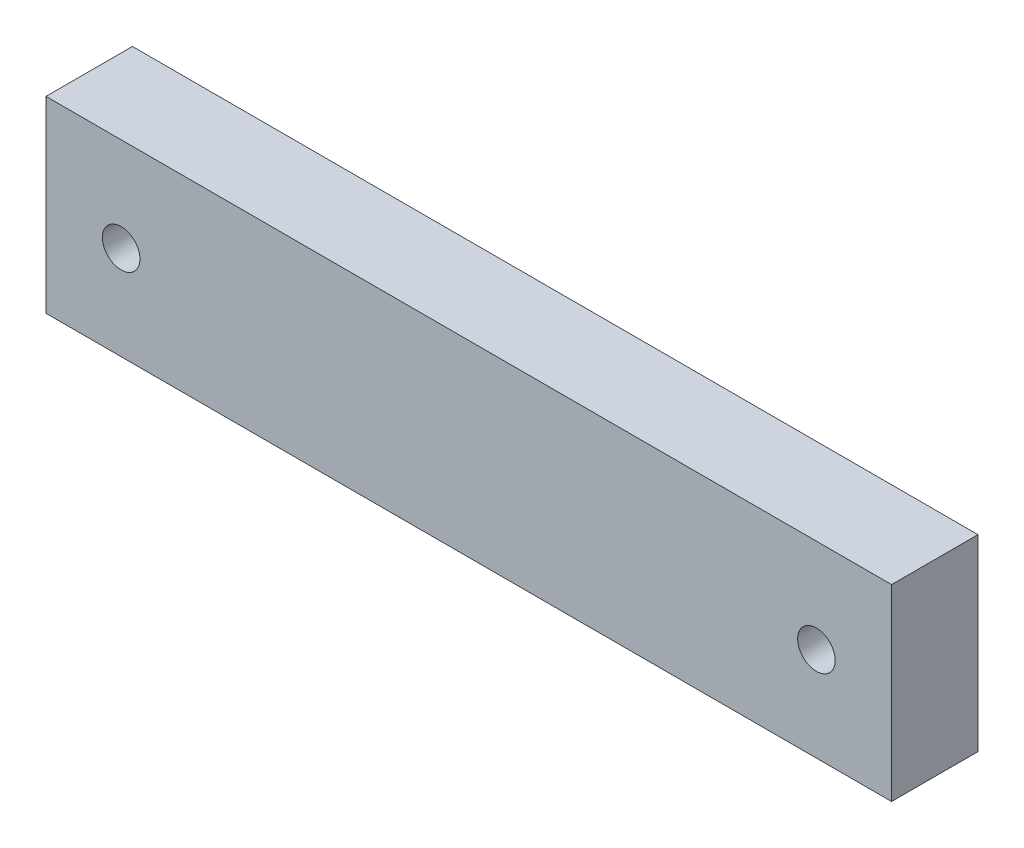
SolidWorks part; units mm, degrees
ref_plane "Front Plane" through (0, 0, 0) normal (0, 0, 1) x (1, 0, 0)
ref_plane "Top Plane" through (0, 0, 0) normal (0, 1, 0) x (1, 0, 0)
ref_plane "Right Plane" through (0, 0, 0) normal (1, 0, 0) x (0, 0, -1)
sketch "Sketch1" plane through (0, 0, 0) normal (0, 0, 1) x (1, 0, 0)
  line L0 (146.7329, 0) -> (-136.6434, 0) construction
  line L1 (-112.5, 25) -> (112.5, 25)
  line L2 (-112.5, 25) -> (-112.5, -25)
  line L3 (-112.5, -25) -> (112.5, -25)
  line L4 (112.5, 25) -> (112.5, -25)
  line L5 (-112.5, 25) -> (112.5, -25) construction
  line L6 (-112.5, -25) -> (112.5, 25) construction
  circle A0 centre (92.5, 0) radius 5
  circle A1 centre (-92.5, 0) radius 5
  point P0 (0, 0)
  dimension "D3" = 10
  dimension "D5" = 20
  dimension "D1" = 225
  dimension "D2" = 50
  dimension "D4" = 20
extrude "Boss-Extrude1" add sketch "Sketch1" along normal blind 23
